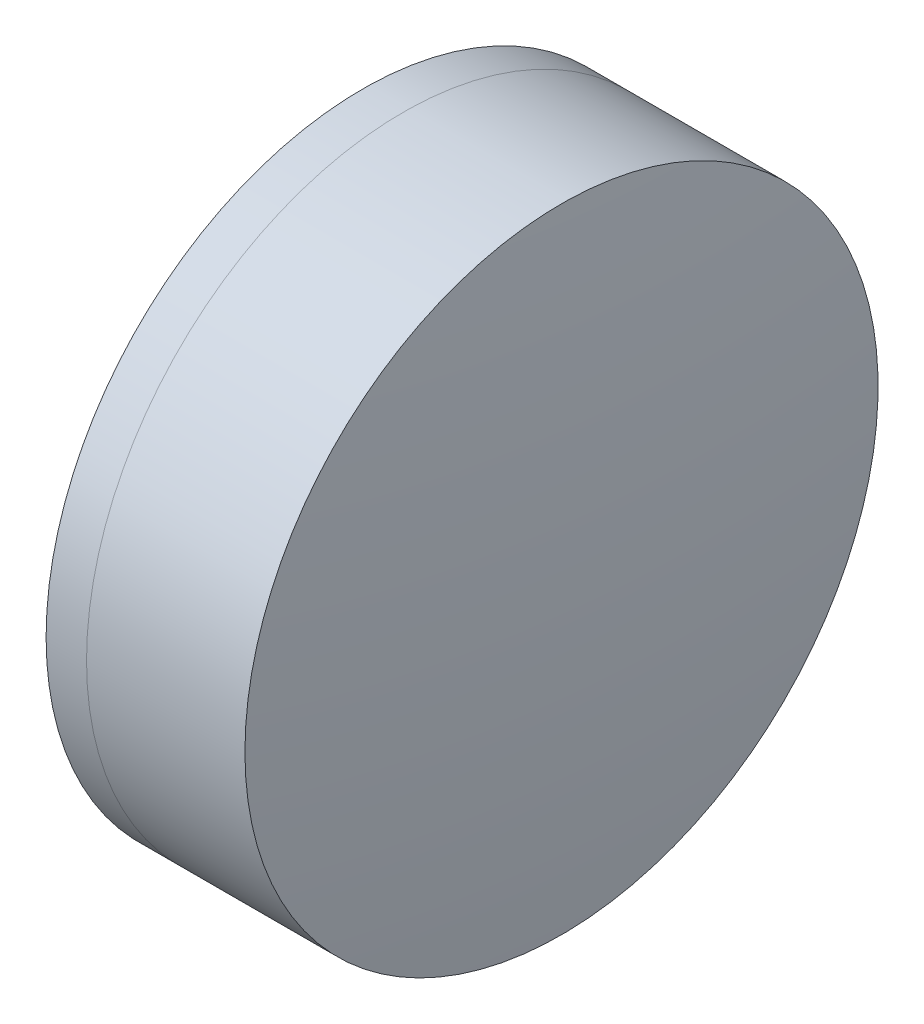
SolidWorks part; units mm, degrees
ref_plane "前视基准面" through (0, 0, 0) normal (0, 0, 1) x (1, 0, 0)
ref_plane "上视基准面" through (0, 0, 0) normal (0, 1, 0) x (1, 0, 0)
ref_plane "右视基准面" through (0, 0, 0) normal (1, 0, 0) x (0, 0, -1)
sketch "草图1" plane through (0, 0, 0) normal (0, 1, 0) x (1, 0, 0)
  line L0 (-9.7026, 0) -> (11.7646, 0) construction
  line L1 (-0.951, -6.35) -> (-0.1401, -6.35)
  line L2 (-0.951, 6.35) -> (-0.1401, 6.35)
  arc A0 (-0.1401, -6.35) -> (-0.1401, 6.35) centre (-9.1222, 0) ccw
  arc A1 (-0.951, 6.35) -> (-0.951, -6.35) centre (10.2778, 0) ccw
  point P10 (-2.6222, 0)
  point P11 (1.8778, 0)
  dimension "D3" = 12.9
  dimension "D4" = 11
  dimension "D1" = 6.35
  dimension "D2" = 6.35
  dimension "D5" = 4.5
revolve "旋转1" add sketch "草图1" angle 360 about L0
sketch "草图2" plane through (0, 0, 0) normal (0, 1, 0) x (1, 0, 0)
  line L0 (-0.5519, 0) -> (13.3053, 0) construction
  line L2 (-0.1401, 6.35) -> (3.0369, 6.35)
  line L3 (-0.1401, -6.35) -> (3.0369, -6.35)
  arc A0 (3.0369, -6.35) -> (3.0369, 6.35) centre (-55.9222, 0) ccw
  arc A1 (-0.1401, -6.35) -> (-0.1401, 6.35) centre (-9.1222, 0) ccw construction
  arc A2 (-0.1401, -6.35) -> (-0.1401, 6.35) centre (-9.1222, 0) ccw
  point P4 (1.8778, 0)
  point P8 (3.3778, 0)
  dimension "D1" = 59.3
  dimension "D2" = 1.5
revolve "旋转3" add sketch "草图2" angle 360 about L0
